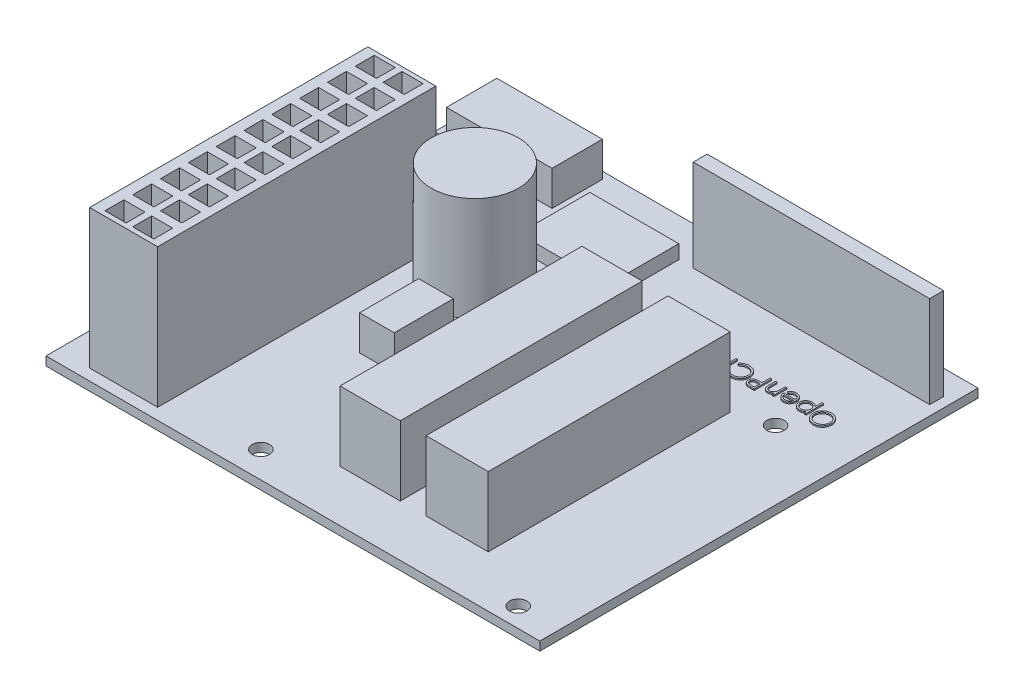
SolidWorks part; units mm, degrees
ref_plane "Front Plane" through (0, 0, 0) normal (0, 0, 1) x (1, 0, 0)
ref_plane "Top Plane" through (0, 0, 0) normal (0, 1, 0) x (1, 0, 0)
ref_plane "Right Plane" through (0, 0, 0) normal (1, 0, 0) x (0, 0, -1)
sketch "Sketch4" plane through (0, 0, 0) normal (0, 1, 0) x (1, 0, 0)
  line L1 (-122.7525, -46.3679) -> (-32.5825, -46.3679)
  line L2 (-122.7525, -46.3679) -> (-122.7525, 33.6421)
  line L3 (-122.7525, 33.6421) -> (-32.5825, 33.6421)
  line L4 (-32.5825, -46.3679) -> (-32.5825, 33.6421)
  dimension "D1" = 90.17
  dimension "D2" = 80.01
extrude "PCB" add sketch "Sketch4" along normal blind 1.6002
sketch "Sketch18" plane through (0, 1.6002, 0) normal (0, 1, 0) x (1, 0, 0)
  line L1 (-116.8384, 6.4967) -> (-116.8384, -44.3033)
  line L2 (-116.8384, 6.4967) -> (-104.4305, 6.4967)
  line L3 (-104.4305, 6.4967) -> (-104.4305, -44.3033)
  line L4 (-116.8384, -44.3033) -> (-104.4305, -44.3033)
  dimension "D1" = 50.8
extrude "ATX plug" add sketch "Sketch18" along normal blind 25.4
sketch "Sketch19" plane through (0, 1.6002, 0) normal (0, 1, 0) x (1, 0, 0)
  line L1 (-119.151, 23.1581) -> (-99.8747, 23.1581)
  line L2 (-119.151, 23.1581) -> (-119.151, 32.3548)
  line L3 (-119.151, 32.3548) -> (-99.8747, 32.3548)
  line L4 (-99.8747, 23.1581) -> (-99.8747, 32.3548)
extrude "Terminal block (peltier, lid heater, lid thermistor)" add sketch "Sketch19" along normal blind 6.35
sketch "Sketch20" plane through (0, 1.6002, 0) normal (0, 1, 0) x (1, 0, 0)
  line L1 (-77.5507, 29.1482) -> (-34.3707, 29.1482)
  line L2 (-77.5507, 29.1482) -> (-77.5507, 26.6082)
  line L3 (-77.5507, 26.6082) -> (-34.3707, 26.6082)
  line L4 (-34.3707, 29.1482) -> (-34.3707, 26.6082)
  dimension "D1" = 43.18
  dimension "D2" = 2.54
extrude "LCD ribbon headers" add sketch "Sketch20" along normal blind 16.764
sketch "Sketch21" plane through (0, 1.6002, 0) normal (0, 1, 0) x (1, 0, 0)
  line L1 (-118.9515, 18.2314) -> (-109.4929, 18.2314)
  line L2 (-118.9515, 18.2314) -> (-118.9515, 12.1991)
  line L3 (-118.9515, 12.1991) -> (-109.4929, 12.1991)
  line L4 (-109.4929, 18.2314) -> (-109.4929, 12.1991)
extrude "2 pin block thermistor plug" add sketch "Sketch21" along normal blind 6.35
sketch "Sketch23" plane through (0, 1.6002, 0) normal (0, 1, 0) x (1, 0, 0)
  line L1 (-94.5981, -6.4719) -> (-88.2623, -6.4719)
  line L2 (-94.5981, -6.4719) -> (-94.5981, -17.2593)
  line L3 (-94.5981, -17.2593) -> (-88.2623, -17.2593)
  line L4 (-88.2623, -6.4719) -> (-88.2623, -17.2593)
extrude "3 pin Fan plug" add sketch "Sketch23" along normal blind 6.35
sketch "Sketch24" plane through (0, 1.6002, 0) normal (0, 1, 0) x (1, 0, 0)
  line L1 (-57.4859, 26.1251) -> (-46.3685, 26.1251)
  line L2 (-57.4859, 26.1251) -> (-57.4859, 20.05)
  line L3 (-57.4859, 20.05) -> (-46.3685, 20.05)
  line L4 (-46.3685, 26.1251) -> (-46.3685, 20.05)
extrude "2 pin terminal for ATX power switch" [suppressed] add sketch "Sketch24" along normal blind 6.35
sketch "Sketch26" plane through (0, 1.6002, 0) normal (0, 1, 0) x (1, 0, 0)
  circle A0 centre (-95.0518, 4.2391) radius 7.9644
extrude "Boss-Extrude1" add sketch "Sketch26" along normal blind 19.05
sketch "Sketch27" plane through (0, 1.6002, 0) normal (0, 1, 0) x (1, 0, 0)
  line L1 (-78.4618, 7.2078) -> (-67.46, 7.2078)
  line L2 (-78.4618, 7.2078) -> (-78.4618, -36.974)
  line L3 (-78.4618, -36.974) -> (-67.46, -36.974)
  line L4 (-67.46, 7.2078) -> (-67.46, -36.974)
  line L5 (-62.745, -36.974) -> (-51.3939, -36.974)
  line L6 (-62.745, -36.974) -> (-62.745, 7.2078)
  line L7 (-62.745, 7.2078) -> (-51.3939, 7.2078)
  line L8 (-51.3939, -36.974) -> (-51.3939, 7.2078)
extrude "Boss-Extrude2" add sketch "Sketch27" along normal blind 12.7
sketch "Sketch28" plane through (0, 1.6002, 0) normal (0, 1, 0) x (1, 0, 0)
  line L1 (-96.4246, 26.6082) -> (-80.189, 26.6082)
  line L2 (-96.4246, 26.6082) -> (-96.4246, 13.6197)
  line L3 (-96.4246, 13.6197) -> (-80.189, 13.6197)
  line L4 (-80.189, 26.6082) -> (-80.189, 13.6197)
extrude "Boss-Extrude3" add sketch "Sketch28" along normal blind 2.54
sketch "Sketch29" plane through (0, 27.0002, 0) normal (0, 1, 0) x (1, 0, 0)
  line L0 (-109.8417, 5.73) -> (-109.8417, 2.2799)
  line L1 (-114.9217, 5.73) -> (-111.0657, 5.73)
  line L2 (-114.9217, 5.73) -> (-114.9217, 2.2799)
  line L3 (-114.9217, 2.2799) -> (-111.0657, 2.2799)
  line L4 (-111.0657, 5.73) -> (-111.0657, 2.2799)
  line L5 (-109.8417, 5.73) -> (-105.9857, 5.73)
  line L6 (-105.9857, 5.73) -> (-105.9857, 2.2799)
  line L7 (-109.8417, 2.2799) -> (-105.9857, 2.2799)
  line L8 (-114.9217, 0.65) -> (-114.9217, -2.8001)
  line L9 (-114.9217, 0.65) -> (-111.0657, 0.65)
  line L10 (-111.0657, 0.65) -> (-111.0657, -2.8001)
  line L11 (-114.9217, -2.8001) -> (-111.0657, -2.8001)
  line L12 (-109.8417, 0.65) -> (-109.8417, -2.8001)
  line L13 (-109.8417, 0.65) -> (-105.9857, 0.65)
  line L14 (-105.9857, 0.65) -> (-105.9857, -2.8001)
  line L15 (-109.8417, -2.8001) -> (-105.9857, -2.8001)
  line L16 (-114.9217, -4.43) -> (-114.9217, -7.8801)
  line L17 (-114.9217, -4.43) -> (-111.0657, -4.43)
  line L18 (-111.0657, -4.43) -> (-111.0657, -7.8801)
  line L19 (-114.9217, -7.8801) -> (-111.0657, -7.8801)
  line L20 (-109.8417, -4.43) -> (-109.8417, -7.8801)
  line L21 (-109.8417, -4.43) -> (-105.9857, -4.43)
  line L22 (-105.9857, -4.43) -> (-105.9857, -7.8801)
  line L23 (-109.8417, -7.8801) -> (-105.9857, -7.8801)
  line L24 (-114.9217, -9.51) -> (-114.9217, -12.9601)
  line L25 (-114.9217, -9.51) -> (-111.0657, -9.51)
  line L26 (-111.0657, -9.51) -> (-111.0657, -12.9601)
  line L27 (-114.9217, -12.9601) -> (-111.0657, -12.9601)
  line L28 (-109.8417, -9.51) -> (-109.8417, -12.9601)
  line L29 (-109.8417, -9.51) -> (-105.9857, -9.51)
  line L30 (-105.9857, -9.51) -> (-105.9857, -12.9601)
  line L31 (-109.8417, -12.9601) -> (-105.9857, -12.9601)
  line L32 (-114.9217, -14.59) -> (-114.9217, -18.0401)
  line L33 (-114.9217, -14.59) -> (-111.0657, -14.59)
  line L34 (-111.0657, -14.59) -> (-111.0657, -18.0401)
  line L35 (-114.9217, -18.0401) -> (-111.0657, -18.0401)
  line L36 (-109.8417, -14.59) -> (-109.8417, -18.0401)
  line L37 (-109.8417, -14.59) -> (-105.9857, -14.59)
  line L38 (-105.9857, -14.59) -> (-105.9857, -18.0401)
  line L39 (-109.8417, -18.0401) -> (-105.9857, -18.0401)
  line L40 (-114.9217, -19.67) -> (-114.9217, -23.1201)
  line L41 (-114.9217, -19.67) -> (-111.0657, -19.67)
  line L42 (-111.0657, -19.67) -> (-111.0657, -23.1201)
  line L43 (-114.9217, -23.1201) -> (-111.0657, -23.1201)
  line L44 (-109.8417, -19.67) -> (-109.8417, -23.1201)
  line L45 (-109.8417, -19.67) -> (-105.9857, -19.67)
  line L46 (-105.9857, -19.67) -> (-105.9857, -23.1201)
  line L47 (-109.8417, -23.1201) -> (-105.9857, -23.1201)
  line L48 (-114.9217, -24.75) -> (-114.9217, -28.2001)
  line L49 (-114.9217, -24.75) -> (-111.0657, -24.75)
  line L50 (-111.0657, -24.75) -> (-111.0657, -28.2001)
  line L51 (-114.9217, -28.2001) -> (-111.0657, -28.2001)
  line L52 (-109.8417, -24.75) -> (-109.8417, -28.2001)
  line L53 (-109.8417, -24.75) -> (-105.9857, -24.75)
  line L54 (-105.9857, -24.75) -> (-105.9857, -28.2001)
  line L55 (-109.8417, -28.2001) -> (-105.9857, -28.2001)
  line L56 (-114.9217, -29.83) -> (-114.9217, -33.2801)
  line L57 (-114.9217, -29.83) -> (-111.0657, -29.83)
  line L58 (-111.0657, -29.83) -> (-111.0657, -33.2801)
  line L59 (-114.9217, -33.2801) -> (-111.0657, -33.2801)
  line L60 (-109.8417, -29.83) -> (-109.8417, -33.2801)
  line L61 (-109.8417, -29.83) -> (-105.9857, -29.83)
  line L62 (-105.9857, -29.83) -> (-105.9857, -33.2801)
  line L63 (-109.8417, -33.2801) -> (-105.9857, -33.2801)
  line L64 (-114.9217, -34.91) -> (-114.9217, -38.3601)
  line L65 (-114.9217, -34.91) -> (-111.0657, -34.91)
  line L66 (-111.0657, -34.91) -> (-111.0657, -38.3601)
  line L67 (-114.9217, -38.3601) -> (-111.0657, -38.3601)
  line L68 (-109.8417, -34.91) -> (-109.8417, -38.3601)
  line L69 (-109.8417, -34.91) -> (-105.9857, -34.91)
  line L70 (-105.9857, -34.91) -> (-105.9857, -38.3601)
  line L71 (-109.8417, -38.3601) -> (-105.9857, -38.3601)
  line L72 (-114.9217, -39.99) -> (-114.9217, -43.4401)
  line L73 (-114.9217, -39.99) -> (-111.0657, -39.99)
  line L74 (-111.0657, -39.99) -> (-111.0657, -43.4401)
  line L75 (-114.9217, -43.4401) -> (-111.0657, -43.4401)
  line L76 (-109.8417, -39.99) -> (-109.8417, -43.4401)
  line L77 (-109.8417, -39.99) -> (-105.9857, -39.99)
  line L78 (-105.9857, -39.99) -> (-105.9857, -43.4401)
  line L79 (-109.8417, -43.4401) -> (-105.9857, -43.4401)
  dimension "D1" = 2
  dimension "D2" = 10
extrude "Cut-Extrude1" cut sketch "Sketch29" against normal blind 12.7
sketch "Sketch30" plane through (0, 1.6002, 0) normal (0, 1, 0) x (-1, 0, 0)
  text T0 "OpenPCR"
extrude "Boss-Extrude4" add sketch "Sketch30" along normal blind 0.254
sketch "Sketch36" plane through (-0.242, 0, 6.0509) normal (0, 1, 0) x (1, 0, 0)
  line L1 (-122.5105, 39.693) -> (-122.5105, -40.317) construction
  line L2 (-32.3405, 39.693) -> (-122.5105, 39.693) construction
  circle A0 centre (-88.1962, 11.925) radius 0.508
  circle A1 centre (-88.1962, 9.385) radius 0.508
  circle A2 centre (-88.1962, 6.845) radius 0.508
  circle A3 centre (-88.1962, 4.305) radius 0.508
  circle A4 centre (-88.1962, 1.765) radius 0.508
  circle A5 centre (-88.1962, -0.775) radius 0.508
  circle A6 centre (-88.1962, -3.315) radius 0.508
  circle A7 centre (-88.1962, -5.855) radius 0.508
  circle A8 centre (-88.1962, -9.919) radius 0.508
  circle A9 centre (-88.1962, -12.459) radius 0.508
  circle A10 centre (-88.1962, -14.999) radius 0.508
  circle A11 centre (-88.1962, -17.539) radius 0.508
  circle A12 centre (-88.1962, -20.079) radius 0.508
  circle A13 centre (-88.1962, -22.619) radius 0.508
  circle A14 centre (-88.1962, -25.159) radius 0.508
  circle A15 centre (-88.1962, -27.699) radius 0.508
  circle A16 centre (-39.9362, 11.925) radius 0.508
  circle A17 centre (-39.9362, -5.855) radius 0.508
  circle A18 centre (-39.9362, 9.385) radius 0.508
  circle A19 centre (-39.9362, -8.395) radius 0.508
  circle A20 centre (-39.9362, 6.845) radius 0.508
  circle A21 centre (-39.9362, -10.935) radius 0.508
  circle A22 centre (-39.9362, 4.305) radius 0.508
  circle A23 centre (-39.9362, -13.475) radius 0.508
  circle A24 centre (-39.9362, 1.765) radius 0.508
  circle A25 centre (-39.9362, -16.015) radius 0.508
  circle A26 centre (-39.9362, -0.775) radius 0.508
  circle A27 centre (-39.9362, -18.555) radius 0.508
extrude "Boss-Extrude8" add sketch "Sketch36" against normal blind 6.35
sketch "Sketch25" plane through (0, 0, 0) normal (0, -1, 0) x (1, 0, 0)
  line L2 (-89.7325, 36.1747) -> (-89.7325, -7.5746)
  line L3 (-89.7325, -7.5746) -> (-87.1925, -7.5746)
  line L4 (-87.1925, 36.1747) -> (-87.1925, -7.5746)
  line L5 (-41.4725, 25.318) -> (-38.9325, 25.318)
  line L6 (-41.4725, 25.318) -> (-41.4725, -7.4478)
  line L7 (-41.4725, -7.4478) -> (-38.9325, -7.4478)
  line L8 (-38.9325, 25.318) -> (-38.9325, -7.4478)
  line L9 (-89.7325, 36.1747) -> (-87.1925, 36.1747)
  dimension "D1" = 45.72
  dimension "D3" = 2.54
extrude "Extrusion for headers" add sketch "Sketch25" along normal blind 2.54
sketch "Sketch39" plane through (0, 1.6002, 0) normal (0, 1, 0) x (1, 0, 0)
  line L0 (-32.5825, -46.3679) -> (-32.5825, 33.6421) construction
  circle A0 centre (-45.1652, 9.2581) radius 1.5875
  circle A2 centre (-88.3452, -41.5419) radius 1.5875
  circle A3 centre (-40.0852, -42.8119) radius 1.5875
  circle A4 centre (-120.3492, -13.3479) radius 1.5875
  point P12 (-38.5095, -42.6187)
  dimension "D1" = 3.175
  dimension "D3" = 3.175
  dimension "D4" = 29.464
  dimension "D5" = 80.264
  dimension "D6" = 7.5027
extrude "Arduino holes" cut sketch "Sketch39" against normal up to next
